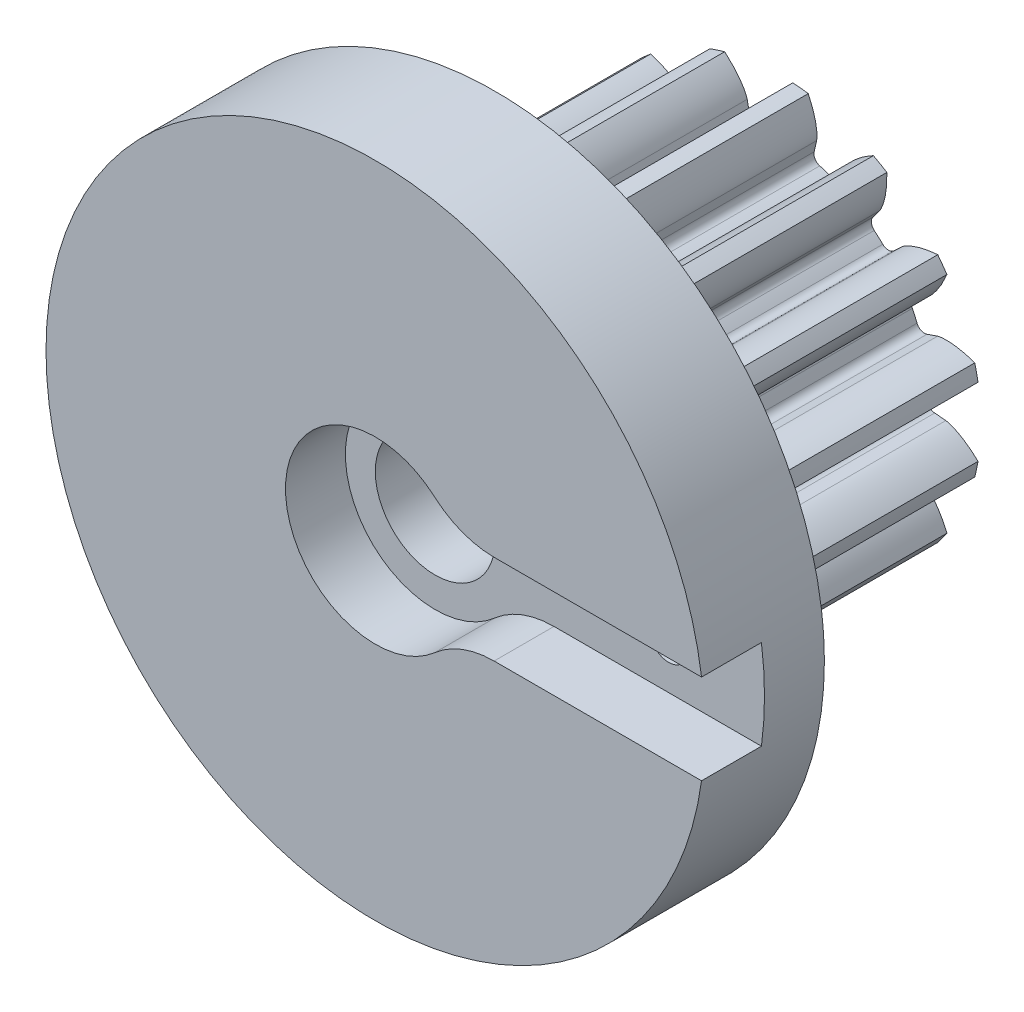
SolidWorks part; units mm, degrees
ref_plane "Front Plane" through (0, 0, 0) normal (0, 0, 1) x (1, 0, 0)
ref_plane "Top Plane" through (0, 0, 0) normal (0, 1, 0) x (1, 0, 0)
ref_plane "Right Plane" through (0, 0, 0) normal (1, 0, 0) x (0, 0, -1)
sketch "Sketch1" plane through (0, 0, 0) normal (0, 0, 1) x (1, 0, 0)
  line L0 (0, 0) -> (0, 7.9375) construction
  line L1 (-2.5511, 8.866) -> (2.5511, 7.009) construction
  circle A0 centre (0, 0) radius 6.6146 construction
  circle A1 centre (0, 0) radius 8.9958 construction
  circle A2 centre (0, 0) radius 7.9375 construction
  circle A3 centre (0, 0) radius 7.4588 construction
  circle A4 centre (0, 0) radius 2.3813 construction
  circle A5 centre (0, 0) radius 6.35 construction
  point P8 (304.8, 0)
  point P13 (190.5, 0)
  dimension "OD | Outside Diameter" = 17.9917
  dimension "Root Diameter" = 13.2292
  dimension "Gear Pitch Diameter" = 15.875
  dimension "Base Diameter" = 14.9176
  dimension "For Shaft Diameter" = 4.7625
  dimension "Hub Diameter" = 12.7
  dimension "Pressure Angle" = 20
  dimension "Number of Teeth" = 381
  dimension "Gear Pitch | Diametral Pitch" = 609.6
sketch "Sketch2" plane through (0, 0, 0) normal (1, 0, 0) x (0, 0, -1)
  line L0 (-6.35, 0) -> (6.35, 0) construction
  line L1 (-6.35, 8.9958) -> (6.35, 8.9958) construction
  point P2 (0, 8.9958)
  point P4 (0, 0)
  point P6 (0, 8.9958)
  dimension "Overall Width" = 12.7
  dimension "Hub Width" = 6.35
  dimension "Face Width" = 6.35
sketch "Sketch3" plane through (0, 0, 0) normal (0, 0, 1) x (1, 0, 0)
  circle A0 centre (0, 0) radius 8.9958
  circle A1 centre (0, 0) radius 8.9958 construction
extrude "Boss-Extrude1" add sketch "Sketch3" against normal blind 12.7
sketch "Sketch4" plane through (0, 0, 0) normal (0, 0, 1) x (1, 0, 0)
  line L0 (0, 0) -> (6.5879, 0.5933) construction
  line L2 (0, 0) -> (6.5879, -0.5933) construction
  line L4 (6.5879, 0.5933) -> (7.4287, 0.669)
  line L5 (7.4287, -0.669) -> (6.5879, -0.5933)
  arc A0 (6.5879, 0.5933) -> (6.5879, -0.5933) centre (0, 0) cw
  arc A3 (8.8649, 1.5293) -> (8.8649, -1.5293) centre (0, 0) cw
  circle A4 centre (0, 0) radius 8.9958 construction
  spline S0 degree 4 poles (7.4287, 0.669) (7.4312, 0.6693) (7.4382, 0.6701) (7.4514, 0.6721) (7.4727, 0.6761) (7.4999, 0.682) (7.5347, 0.6906) (7.5755, 0.7021) (7.6201, 0.7162) (7.6683, 0.7329) (7.716, 0.751) (7.7633, 0.7701) (7.8102, 0.7904) (7.8665, 0.8161) (7.9336, 0.8488) (8.0112, 0.8895) (8.0982, 0.9387) (8.1857, 0.9921) (8.2709, 1.0472) (8.3557, 1.1058) (8.437, 1.1646) (8.5201, 1.2287) (8.5962, 1.2894) (8.68, 1.3607) (8.7471, 1.4191) (8.8341, 1.4996) (8.8849, 1.5482) (8.9438, 1.6062) (8.9696, 1.6325) (8.9855, 1.6488) knots 0 0 0 0 0 0.005377 0.015084 0.028532 0.04661 0.064855 0.092111 0.119476 0.146842 0.174209 0.201575 0.228941 0.256307 0.307035 0.361767 0.4165 0.471232 0.525964 0.580697 0.635429 0.690161 0.744894 0.799626 0.854358 0.909091 0.954545 1 1 1 1 1 construction
  spline S1 degree 4 poles (7.4287, 0.669) (7.4312, 0.6693) (7.4382, 0.6701) (7.4514, 0.6721) (7.4727, 0.6761) (7.4999, 0.682) (7.5347, 0.6906) (7.5755, 0.7021) (7.6201, 0.7162) (7.6683, 0.7329) (7.716, 0.751) (7.7633, 0.7701) (7.8102, 0.7904) (7.8665, 0.8161) (7.9336, 0.8488) (8.0112, 0.8895) (8.0982, 0.9387) (8.1857, 0.9921) (8.2709, 1.0472) (8.3557, 1.1058) (8.437, 1.1646) (8.5201, 1.2287) (8.5962, 1.2894) (8.68, 1.3607) (8.7471, 1.4191) (8.8152, 1.4821) (8.8481, 1.5132) (8.8649, 1.5293) knots 0 0 0 0 0 0.005377 0.015084 0.028532 0.04661 0.064855 0.092111 0.119476 0.146842 0.174209 0.201575 0.228941 0.256307 0.307035 0.361767 0.4165 0.471232 0.525964 0.580697 0.635429 0.690161 0.744894 0.799626 0.854358 0.909091 0.909091 0.909091 0.909091 0.909091
  spline S2 degree 4 poles (7.4287, -0.669) (7.4312, -0.6693) (7.4382, -0.6701) (7.4514, -0.6721) (7.4727, -0.6761) (7.4999, -0.682) (7.5347, -0.6906) (7.5755, -0.7021) (7.6201, -0.7162) (7.6683, -0.7329) (7.716, -0.751) (7.7633, -0.7701) (7.8102, -0.7904) (7.8665, -0.8161) (7.9336, -0.8488) (8.0112, -0.8895) (8.0982, -0.9387) (8.1857, -0.9921) (8.2709, -1.0472) (8.3557, -1.1058) (8.437, -1.1646) (8.5201, -1.2287) (8.5962, -1.2894) (8.68, -1.3607) (8.7471, -1.4191) (8.8341, -1.4996) (8.8849, -1.5482) (8.9438, -1.6062) (8.9696, -1.6325) (8.9855, -1.6488) knots 0 0 0 0 0 0.005377 0.015084 0.028532 0.04661 0.064855 0.092111 0.119476 0.146842 0.174209 0.201575 0.228941 0.256307 0.307035 0.361767 0.4165 0.471232 0.525964 0.580697 0.635429 0.690161 0.744894 0.799626 0.854358 0.909091 0.954545 1 1 1 1 1 construction
  spline S3 degree 4 poles (7.4287, -0.669) (7.4312, -0.6693) (7.4382, -0.6701) (7.4514, -0.6721) (7.4727, -0.6761) (7.4999, -0.682) (7.5347, -0.6906) (7.5755, -0.7021) (7.6201, -0.7162) (7.6683, -0.7329) (7.716, -0.751) (7.7633, -0.7701) (7.8102, -0.7904) (7.8665, -0.8161) (7.9336, -0.8488) (8.0112, -0.8895) (8.0982, -0.9387) (8.1857, -0.9921) (8.2709, -1.0472) (8.3557, -1.1058) (8.437, -1.1646) (8.5201, -1.2287) (8.5962, -1.2894) (8.68, -1.3607) (8.7471, -1.4191) (8.8152, -1.4821) (8.8481, -1.5132) (8.8649, -1.5293) knots 0 0 0 0 0 0.005377 0.015084 0.028532 0.04661 0.064855 0.092111 0.119476 0.146842 0.174209 0.201575 0.228941 0.256307 0.307035 0.361767 0.4165 0.471232 0.525964 0.580697 0.635429 0.690161 0.744894 0.799626 0.854358 0.909091 0.909091 0.909091 0.909091 0.909091
  dimension "D1" = 13.2292
extrude "Cut-Extrude1" cut sketch "Sketch4" against normal through all both and the other way through all
fillet "Fillet1" radius 0.3551 2 edges at (6.5879, -0.5933, -6.35) (6.5879, 0.5933, -6.35)
pattern_circular "CirPattern1" count 15 over 360 about axis through (0, 0, 6.35) along (0, 0, -1) of "Cut-Extrude1", "Fillet1"
scale "Scale1" scale about centroid uniform scaling yes scale factor 1.9
sketch "Sketch12" plane through (0, 0, 5.715) normal (0, 0, 1) x (1, 0, 0)
  circle A0 centre (0, 0) radius 27.94
  dimension "D1" = 55.88
extrude "Boss-Extrude3" add sketch "Sketch12" along normal blind 10.16
sketch "Sketch13" plane through (0, 0, 15.875) normal (0, 0, 1) x (1, 0, 0)
  circle A0 centre (0, 0) radius 5.08
extrude "Cut-Extrude6" cut sketch "Sketch13" against normal through all
sketch "Sketch14" plane through (0, 0, 15.875) normal (0, 0, 1) x (1, 0, 0)
  line L1 (10.0803, 3.81) -> (29.3447, 3.81)
  line L3 (10.0803, -3.81) -> (29.3447, -3.81)
  line L4 (29.3447, 3.81) -> (29.3447, -3.81)
  arc A0 (5.0402, 5.715) -> (5.0402, -5.715) centre (0, 0) ccw
  arc A1 (5.0402, -5.715) -> (10.0803, -3.81) centre (10.0803, -11.43) cw
  arc A2 (5.0402, 5.715) -> (10.0803, 3.81) centre (10.0803, 11.43) ccw
  point P7 (29.3447, 0)
  dimension "D1" = 15.24
  dimension "D3" = 7.62
  dimension "D2" = 7.62
extrude "Cut-Extrude7" cut sketch "Sketch14" against normal blind 5.08
sketch "Sketch15" plane through (0, 0, 10.795) normal (0, 0, 1) x (1, 0, 0)
  line L0 (0, 0) -> (0, 4.2867) construction
  circle A0 centre (19.812, 0) radius 1.5875
  dimension "D1" = 3.175
  dimension "D2" = 19.812
extrude "Cut-Extrude8" cut sketch "Sketch15" against normal blind 5.08
sketch "Sketch16" plane through (0, 0, 5.715) normal (0, 0, -1) x (-1, 0, 0)
  circle A0 centre (-19.812, 0) radius 2.7496
extrude "Cut-Extrude9" cut sketch "Sketch16" against normal blind 3.81
sketch "Sketch17" plane through (0, 0, -18.415) normal (0, 0, -1) x (-1, 0, 0)
  circle A0 centre (0, 0) radius 7.9375
  dimension "D1" = 15.875
equation "\"Root Diameter@Sketch1\"=\"Root Diameter\""
equation "\"OD | Outside Diameter@Sketch1\"=\"Outside Diameter\""
equation "\"D1@CirPattern1\"=\"Number of Teeth\""
equation "\"Diametral Pitch\"= 24"
equation "\"Number of Teeth\"= 15"
equation "\"Pressure Angle\"=20"
equation "\"Pitch Diameter\"= \"Number of Teeth\" / \"Diametral Pitch\""
equation "\"Base Diameter\"= \"Pitch Diameter\" * cos ( \"Pressure Angle\" )"
equation "\"Outside Diameter\"= ( \"Number of Teeth\" + 2 ) / \"Diametral Pitch\""
equation "\"Dedendum\"= 1.25 / \"Diametral Pitch\""
equation "\"Root Diameter\"= \"Pitch Diameter\" - ( 2 * \"Dedendum\" )"
equation "\"Pitch Angle\"= 360deg / \"Number of Teeth\""
equation "\"Alpha\"= sqr ( \"Pitch Diameter\" ^ 2 - \"Base Diameter\" ^ 2 ) / \"Base Diameter\" * 180 / PI - \"Pressure Angle\""
equation "\"Beta\"= ( \"Pitch Angle\" / 4 - \"Alpha\" )"
equation "\"Phi\"= sqr ( ( \"Outside Diameter\" / 2 ) ^ 2 - ( \"Base Diameter\" / 2 ) ^ 2 ) / ( \"Base Diameter\" / 2 )"
equation "\"Addendum\"= 1 / \"Diametral Pitch\""
equation "\"WorkingDepth\"= 2 / \"Diametral Pitch\""
equation "\"WholeDepth\"= 2.25 / \"Diametral Pitch\""
equation "\"Clearance\"= 0.25 / \"Diametral Pitch\""
equation "\"ToothThickness\"= ( pi * 2 ) / \"Diametral Pitch\""
equation "\"CircularPitch\"= pi / \"Diametral Pitch\""
equation "\"Number of Teeth@Sketch1\"=\"Number of Teeth\""
equation "\"Gear Pitch | Diametral Pitch@Sketch1\"=\"Diametral Pitch\""
equation "\"Pressure Angle@Sketch1\"=\"Pressure Angle\""
equation "\"Gear Pitch Diameter@Sketch1\"=\"Pitch Diameter\""
equation "\"Base Diameter@Sketch1\"=\"Base Diameter\""
equation "\"Fillet\"= \"Clearance\" * cos ( \"Pressure Angle\" ) * tan ( ( 90 + \"Pressure Angle\" ) / 2 )"
equation "\"D1@Fillet1\"=\"Fillet\""
equation "\"D1@Sketch4\"=if( \"Base Diameter\">\"Root Diameter\",\"Root Diameter\",\"Base Diameter\"-.00001)"
equation "\"D1@Fillet2\"=\"Fillet\""
